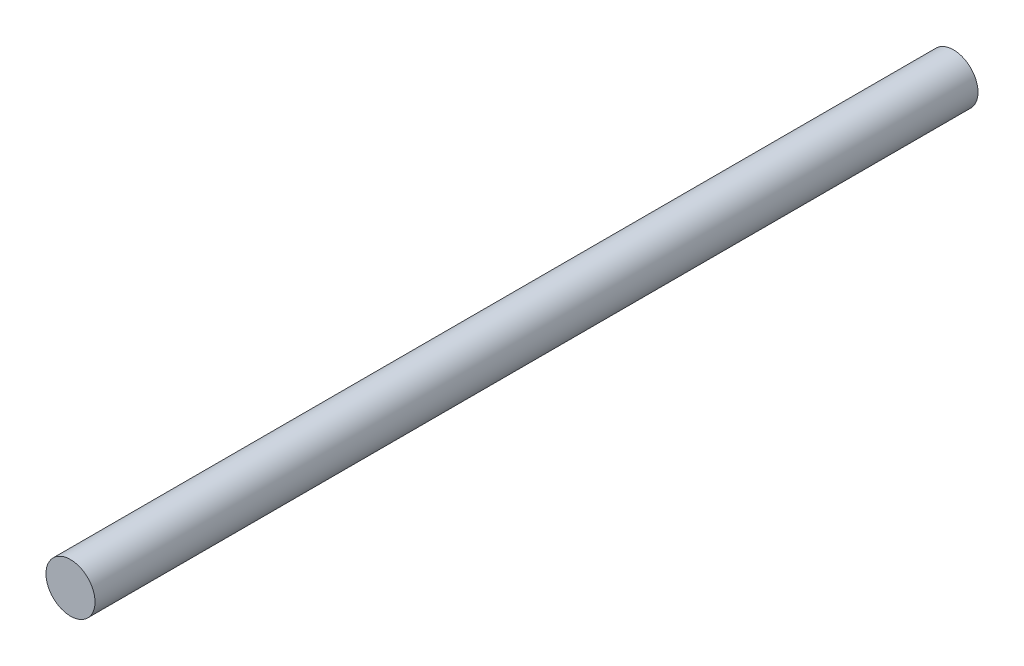
SolidWorks part; units mm, degrees
ref_plane "Front Plane" through (0, 0, 0) normal (0, 0, 1) x (1, 0, 0)
ref_plane "Top Plane" through (0, 0, 0) normal (0, 1, 0) x (1, 0, 0)
ref_plane "Right Plane" through (0, 0, 0) normal (1, 0, 0) x (0, 0, -1)
sketch "Sketch1" plane through (0, 0, 0) normal (0, 0, 1) x (1, 0, 0)
  circle A0 centre (0, 0) radius 3.175
  dimension "D1" = 6.35
extrude "Boss-Extrude1" add sketch "Sketch1" along normal mid plane 114.3
